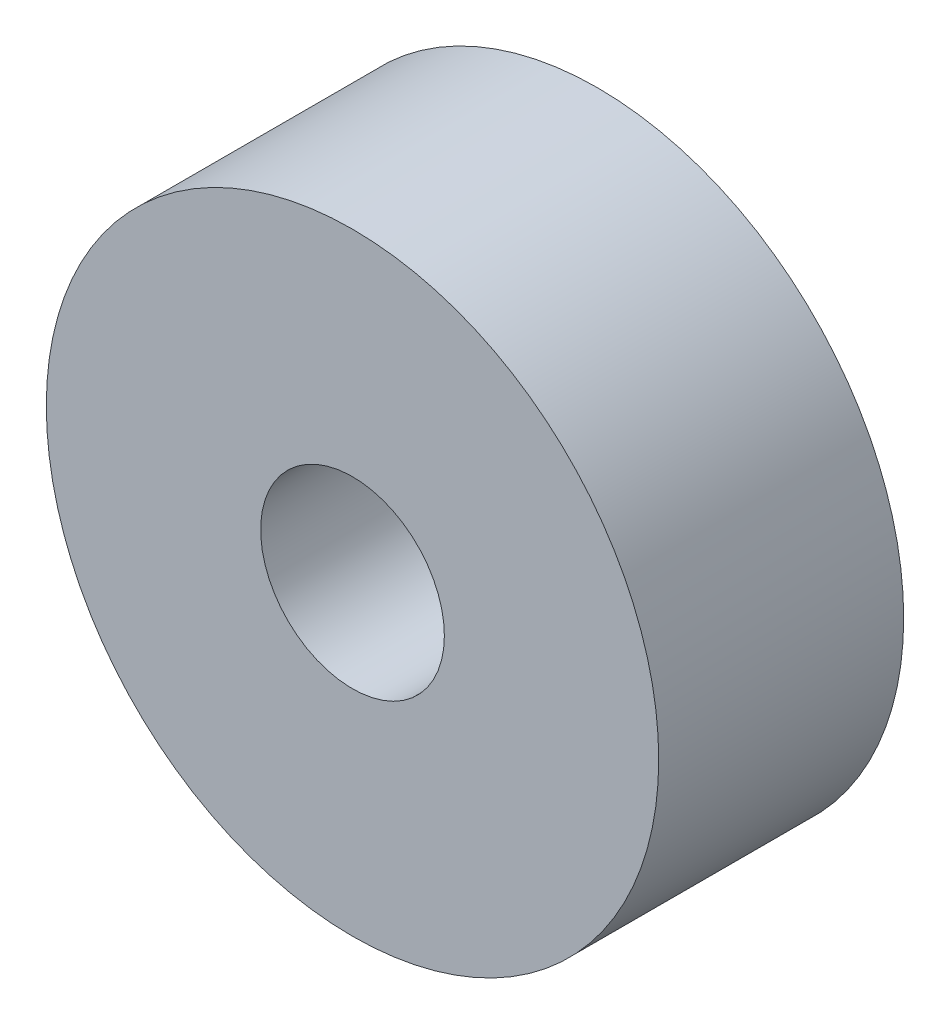
SolidWorks part; units mm, degrees
ref_plane "Plan de face" through (0, 0, 0) normal (0, 0, 1) x (1, 0, 0)
ref_plane "Plan de dessus" through (0, 0, 0) normal (0, 1, 0) x (1, 0, 0)
ref_plane "Plan de droite" through (0, 0, 0) normal (1, 0, 0) x (0, 0, -1)
sketch "Esquisse1" plane through (0, 0, 0) normal (0, 0, 1) x (1, 0, 0)
  circle A0 centre (0, 0) radius 1.5
  circle A1 centre (0, 0) radius 5
  dimension "D1" = 10
  dimension "D2" = 3
extrude "Boss.-Extru.1" add sketch "Esquisse1" along normal blind 4
